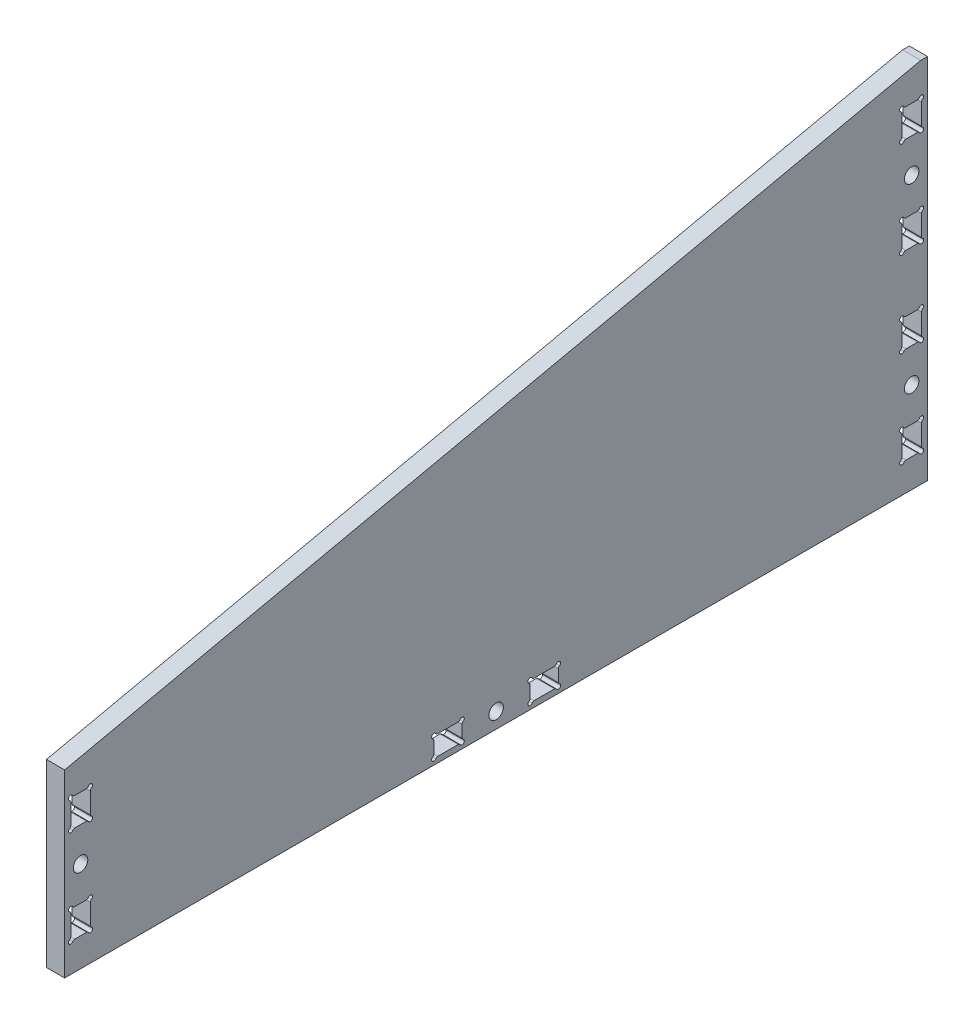
SolidWorks part; units mm, degrees
ref_plane "Alzado" through (0, 0, 0) normal (0, 0, 1) x (1, 0, 0)
ref_plane "Planta" through (0, 0, 0) normal (0, 1, 0) x (1, 0, 0)
ref_plane "Vista lateral" through (0, 0, 0) normal (1, 0, 0) x (0, 0, -1)
sketch "Croquis1" plane through (0, 0, 0) normal (1, 0, 0) x (0, 0, -1)
  line L0 (-94.8108, -1.6532) -> (93.6893, 39.3945)
  line L2 (95.1893, -41.4778) -> (-94.8108, -41.3254)
  line L4 (-1.4107, -37.9765) -> (1.7893, -37.9765) construction
  line L5 (0.1893, -41.4016) -> (0.1893, 19.0339) construction
  line L6 (-91.3108, -20.0603) -> (-91.3108, -22.5929) construction
  line L7 (-93.3108, -21.3266) -> (-89.3108, -21.3266) construction
  line L8 (91.6893, 19.7897) -> (91.6893, 17.2571) construction
  line L9 (89.6893, 18.5234) -> (93.6893, 18.5234) construction
  line L10 (89.6893, -21.4766) -> (93.6893, -21.4766) construction
  line L11 (91.6893, -20.2103) -> (91.6893, -22.7429) construction
  line L12 (13.8893, -36.6926) -> (13.8893, -39.2605)
  line L13 (-93.4607, -8.4926) -> (-93.4607, -12.9606)
  line L22 (-8.1768, -40.1265) -> (-12.6447, -40.1265)
  line L23 (7.6893, -39.2605) -> (7.6893, -36.6926)
  line L24 (-13.5107, -39.2605) -> (-13.5107, -36.6926)
  line L25 (0.1893, -39.9765) -> (0.1893, -35.9765) construction
  line L26 (13.0232, -40.1265) -> (8.5553, -40.1265)
  line L27 (-12.6447, -35.8266) -> (-8.1768, -35.8266)
  line L28 (-7.3107, -36.6926) -> (-7.3107, -39.2605)
  line L29 (8.5553, -35.8266) -> (13.0232, -35.8266)
  line L30 (-94.8108, -41.3266) -> (-94.8108, -1.6532)
  line L31 (95.1893, 39.3945) -> (95.1893, -41.4778)
  line L32 (-90.0268, -13.8266) -> (-92.5947, -13.8266)
  line L34 (93.6893, 39.3945) -> (95.1893, 39.3945)
  line L35 (-89.3108, -21.3266) -> (-93.3108, -21.3266) construction
  line L36 (-92.5947, -7.6266) -> (-90.0268, -7.6266)
  line L40 (-90.0268, -35.0266) -> (-92.5947, -35.0266)
  line L41 (-92.5947, -28.8266) -> (-90.0268, -28.8266)
  line L42 (92.9733, 26.0234) -> (90.4054, 26.0234)
  line L43 (89.5394, 5.6894) -> (89.5394, 10.1574)
  line L44 (93.6893, 18.5234) -> (89.6893, 18.5234) construction
  line L45 (90.4054, 32.2234) -> (92.9733, 32.2234)
  line L46 (89.5394, 26.8894) -> (89.5394, 31.3574)
  line L47 (93.8393, 31.3574) -> (93.8393, 26.8894)
  line L48 (93.8393, 10.1574) -> (93.8393, 5.6894)
  line L49 (92.9733, 4.8234) -> (90.4054, 4.8234)
  line L50 (90.4054, 11.0234) -> (92.9733, 11.0234)
  line L51 (92.9733, -13.9766) -> (90.4054, -13.9766)
  line L52 (89.5394, -34.3106) -> (89.5394, -29.8426)
  line L53 (93.6893, -21.4766) -> (89.6893, -21.4766) construction
  line L54 (90.4054, -7.7766) -> (92.9733, -7.7766)
  line L55 (89.5394, -13.1106) -> (89.5394, -8.6426)
  line L56 (93.8393, -8.6426) -> (93.8393, -13.1106)
  line L57 (93.8393, -29.8426) -> (93.8393, -34.3106)
  line L58 (92.9733, -35.1766) -> (90.4054, -35.1766)
  line L59 (90.4054, -28.9766) -> (92.9733, -28.9766)
  line L60 (-93.4607, -29.6926) -> (-93.4607, -34.1606)
  line L61 (-89.1608, -8.4926) -> (-89.1608, -12.9606)
  line L62 (-89.1608, -29.6926) -> (-89.1608, -34.1606)
  arc A26 (8.5553, -40.1265) -> (8.1223, -40.3765) centre (8.5553, -40.6265) ccw
  arc A27 (8.1223, -35.5766) -> (7.4393, -36.2596) centre (7.6893, -35.8266) ccw
  arc A28 (-12.6447, -40.1265) -> (-13.0777, -40.3765) centre (-12.6447, -40.6265) ccw
  arc A29 (-13.7607, -39.6935) -> (-13.5107, -39.2605) centre (-14.0107, -39.2605) ccw
  arc A30 (7.4393, -39.6935) -> (8.1223, -40.3765) centre (7.6893, -40.1265) ccw
  arc A31 (-7.0607, -36.2596) -> (-7.3107, -36.6926) centre (-6.8107, -36.6926) ccw
  arc A32 (7.4393, -39.6935) -> (7.6893, -39.2605) centre (7.1893, -39.2605) ccw
  circle A33 centre (0.1893, -37.9765) radius 1.6
  arc A34 (7.6893, -36.6926) -> (7.4393, -36.2596) centre (7.1893, -36.6926) ccw
  circle A35 centre (0.1893, -37.9765) radius 2.8 construction
  arc A36 (-8.1768, -35.8266) -> (-7.7437, -35.5766) centre (-8.1768, -35.3266) ccw
  arc A37 (-7.7437, -40.3765) -> (-7.0607, -39.6935) centre (-7.3107, -40.1265) ccw
  arc A38 (8.1223, -35.5766) -> (8.5553, -35.8266) centre (8.5553, -35.3266) ccw
  arc A39 (-7.7437, -40.3765) -> (-8.1768, -40.1265) centre (-8.1768, -40.6265) ccw
  arc A40 (14.1393, -36.2596) -> (13.4563, -35.5766) centre (13.8893, -35.8266) ccw
  arc A41 (14.1393, -36.2596) -> (13.8893, -36.6926) centre (14.3893, -36.6926) ccw
  arc A42 (13.8893, -39.2605) -> (14.1393, -39.6935) centre (14.3893, -39.2605) ccw
  arc A43 (-7.3107, -39.2605) -> (-7.0607, -39.6935) centre (-6.8107, -39.2605) ccw
  arc A44 (-13.0777, -35.5766) -> (-12.6447, -35.8266) centre (-12.6447, -35.3266) ccw
  arc A45 (13.4563, -40.3765) -> (13.0232, -40.1265) centre (13.0232, -40.6265) ccw
  arc A46 (-13.5107, -36.6926) -> (-13.7607, -36.2596) centre (-14.0107, -36.6926) ccw
  arc A47 (13.4563, -40.3765) -> (14.1393, -39.6935) centre (13.8893, -40.1265) ccw
  arc A48 (-13.0777, -35.5766) -> (-13.7607, -36.2596) centre (-13.5107, -35.8266) ccw
  arc A49 (13.0232, -35.8266) -> (13.4563, -35.5766) centre (13.0232, -35.3266) ccw
  arc A50 (-7.0607, -36.2596) -> (-7.7437, -35.5766) centre (-7.3107, -35.8266) ccw
  arc A51 (-13.7607, -39.6935) -> (-13.0777, -40.3765) centre (-13.5107, -40.1265) ccw
  arc A52 (-93.0277, -28.5766) -> (-93.7107, -29.2596) centre (-93.4607, -28.8266) ccw
  arc A53 (-93.4607, -8.4926) -> (-93.7107, -8.0596) centre (-93.9607, -8.4926) ccw
  arc A54 (-90.0268, -28.8266) -> (-89.5938, -28.5766) centre (-90.0268, -28.3266) ccw
  arc A55 (-89.5938, -35.2766) -> (-88.9108, -34.5936) centre (-89.1608, -35.0266) ccw
  circle A56 centre (-91.3108, -21.3266) radius 1.6
  arc A57 (-88.9108, -8.0596) -> (-89.1608, -8.4926) centre (-88.6608, -8.4926) ccw
  arc A58 (-92.5947, -13.8266) -> (-93.0277, -14.0766) centre (-92.5947, -14.3266) ccw
  arc A59 (-93.0277, -7.3766) -> (-92.5947, -7.6266) centre (-92.5947, -7.1266) ccw
  arc A60 (-88.9108, -29.2596) -> (-89.1608, -29.6926) centre (-88.6608, -29.6926) ccw
  arc A61 (-93.7107, -34.5936) -> (-93.4607, -34.1606) centre (-93.9607, -34.1606) ccw
  arc A62 (-89.5938, -14.0766) -> (-88.9108, -13.3936) centre (-89.1608, -13.8266) ccw
  arc A63 (-93.4607, -29.6926) -> (-93.7107, -29.2596) centre (-93.9607, -29.6926) ccw
  arc A64 (-93.0277, -7.3766) -> (-93.7107, -8.0596) centre (-93.4607, -7.6266) ccw
  arc A65 (-92.5947, -35.0266) -> (-93.0277, -35.2766) centre (-92.5947, -35.5266) ccw
  arc A66 (-93.0277, -28.5766) -> (-92.5947, -28.8266) centre (-92.5947, -28.3266) ccw
  arc A67 (-88.9108, -8.0596) -> (-89.5938, -7.3766) centre (-89.1608, -7.6266) ccw
  arc A68 (-89.5938, -35.2766) -> (-90.0268, -35.0266) centre (-90.0268, -35.5266) ccw
  arc A69 (-89.1608, -34.1606) -> (-88.9108, -34.5936) centre (-88.6608, -34.1606) ccw
  arc A70 (-88.9108, -29.2596) -> (-89.5938, -28.5766) centre (-89.1608, -28.8266) ccw
  circle A71 centre (-91.3108, -21.3266) radius 2.8 construction
  arc A72 (-89.1608, -12.9606) -> (-88.9108, -13.3936) centre (-88.6608, -12.9606) ccw
  arc A73 (-89.5938, -14.0766) -> (-90.0268, -13.8266) centre (-90.0268, -14.3266) ccw
  arc A74 (-93.7107, -13.3936) -> (-93.0277, -14.0766) centre (-93.4607, -13.8266) ccw
  arc A75 (-90.0268, -7.6266) -> (-89.5938, -7.3766) centre (-90.0268, -7.1266) ccw
  arc A76 (-93.7107, -34.5936) -> (-93.0277, -35.2766) centre (-93.4607, -35.0266) ccw
  arc A77 (-93.7107, -13.3936) -> (-93.4607, -12.9606) centre (-93.9607, -12.9606) ccw
  arc A78 (89.9724, 11.2734) -> (89.2894, 10.5904) centre (89.5394, 11.0234) ccw
  arc A79 (89.5394, 31.3574) -> (89.2894, 31.7904) centre (89.0394, 31.3574) ccw
  arc A80 (92.9733, 11.0234) -> (93.4063, 11.2734) centre (92.9733, 11.5234) ccw
  arc A81 (93.4063, 4.5734) -> (94.0893, 5.2564) centre (93.8393, 4.8234) ccw
  circle A82 centre (91.6893, 18.5234) radius 1.6
  arc A83 (94.0893, 31.7904) -> (93.8393, 31.3574) centre (94.3393, 31.3574) ccw
  arc A84 (90.4054, 26.0234) -> (89.9724, 25.7734) centre (90.4054, 25.5234) ccw
  arc A85 (89.9724, 32.4734) -> (90.4054, 32.2234) centre (90.4054, 32.7234) ccw
  arc A86 (94.0893, 10.5904) -> (93.8393, 10.1574) centre (94.3393, 10.1574) ccw
  arc A87 (89.2894, 5.2564) -> (89.5394, 5.6894) centre (89.0394, 5.6894) ccw
  arc A88 (93.4063, 25.7734) -> (94.0893, 26.4564) centre (93.8393, 26.0234) ccw
  arc A89 (89.5394, 10.1574) -> (89.2894, 10.5904) centre (89.0394, 10.1574) ccw
  arc A90 (89.9724, 32.4734) -> (89.2894, 31.7904) centre (89.5394, 32.2234) ccw
  arc A91 (90.4054, 4.8234) -> (89.9724, 4.5734) centre (90.4054, 4.3234) ccw
  arc A92 (89.9724, 11.2734) -> (90.4054, 11.0234) centre (90.4054, 11.5234) ccw
  arc A93 (94.0893, 31.7904) -> (93.4063, 32.4734) centre (93.8393, 32.2234) ccw
  arc A94 (93.4063, 4.5734) -> (92.9733, 4.8234) centre (92.9733, 4.3234) ccw
  arc A95 (93.8393, 5.6894) -> (94.0893, 5.2564) centre (94.3393, 5.6894) ccw
  arc A96 (94.0893, 10.5904) -> (93.4063, 11.2734) centre (93.8393, 11.0234) ccw
  circle A97 centre (91.6893, 18.5234) radius 2.8 construction
  arc A98 (93.8393, 26.8894) -> (94.0893, 26.4564) centre (94.3393, 26.8894) ccw
  arc A99 (93.4063, 25.7734) -> (92.9733, 26.0234) centre (92.9733, 25.5234) ccw
  arc A100 (89.2894, 26.4564) -> (89.9724, 25.7734) centre (89.5394, 26.0234) ccw
  arc A101 (92.9733, 32.2234) -> (93.4063, 32.4734) centre (92.9733, 32.7234) ccw
  arc A102 (89.2894, 5.2564) -> (89.9724, 4.5734) centre (89.5394, 4.8234) ccw
  arc A103 (89.2894, 26.4564) -> (89.5394, 26.8894) centre (89.0394, 26.8894) ccw
  arc A104 (89.9724, -28.7266) -> (89.2894, -29.4096) centre (89.5394, -28.9766) ccw
  arc A105 (89.5394, -8.6426) -> (89.2894, -8.2096) centre (89.0394, -8.6426) ccw
  arc A106 (92.9733, -28.9766) -> (93.4063, -28.7266) centre (92.9733, -28.4766) ccw
  arc A107 (93.4063, -35.4266) -> (94.0893, -34.7436) centre (93.8393, -35.1766) ccw
  circle A108 centre (91.6893, -21.4766) radius 1.6
  arc A109 (94.0893, -8.2096) -> (93.8393, -8.6426) centre (94.3393, -8.6426) ccw
  arc A110 (90.4054, -13.9766) -> (89.9724, -14.2266) centre (90.4054, -14.4766) ccw
  arc A111 (89.9724, -7.5266) -> (90.4054, -7.7766) centre (90.4054, -7.2766) ccw
  arc A112 (94.0893, -29.4096) -> (93.8393, -29.8426) centre (94.3393, -29.8426) ccw
  arc A113 (89.2894, -34.7436) -> (89.5394, -34.3106) centre (89.0394, -34.3106) ccw
  arc A114 (93.4063, -14.2266) -> (94.0893, -13.5436) centre (93.8393, -13.9766) ccw
  arc A115 (89.5394, -29.8426) -> (89.2894, -29.4096) centre (89.0394, -29.8426) ccw
  arc A116 (89.9724, -7.5266) -> (89.2894, -8.2096) centre (89.5394, -7.7766) ccw
  arc A117 (90.4054, -35.1766) -> (89.9724, -35.4266) centre (90.4054, -35.6766) ccw
  arc A118 (89.9724, -28.7266) -> (90.4054, -28.9766) centre (90.4054, -28.4766) ccw
  arc A119 (94.0893, -8.2096) -> (93.4063, -7.5266) centre (93.8393, -7.7766) ccw
  arc A120 (93.4063, -35.4266) -> (92.9733, -35.1766) centre (92.9733, -35.6766) ccw
  arc A121 (93.8393, -34.3106) -> (94.0893, -34.7436) centre (94.3393, -34.3106) ccw
  arc A122 (94.0893, -29.4096) -> (93.4063, -28.7266) centre (93.8393, -28.9766) ccw
  circle A123 centre (91.6893, -21.4766) radius 2.8 construction
  arc A124 (93.8393, -13.1106) -> (94.0893, -13.5436) centre (94.3393, -13.1106) ccw
  arc A125 (93.4063, -14.2266) -> (92.9733, -13.9766) centre (92.9733, -14.4766) ccw
  arc A126 (89.2894, -13.5436) -> (89.9724, -14.2266) centre (89.5394, -13.9766) ccw
  arc A127 (92.9733, -7.7766) -> (93.4063, -7.5266) centre (92.9733, -7.2766) ccw
  arc A128 (89.2894, -34.7436) -> (89.9724, -35.4266) centre (89.5394, -35.1766) ccw
  arc A129 (89.2894, -13.5436) -> (89.5394, -13.1106) centre (89.0394, -13.1106) ccw
  point P0 (-93.3108, -1.3266)
  point P2 (93.6893, -41.4766)
  point P3 (-93.3108, -41.3266)
  point P143 (-94.8108, -1.3266)
extrude "Saliente-Extruir1" add sketch "Croquis1" along normal blind 4 contours L34 L0 L30 L2 L31 A128 A113 L52 A115 A104 A118 L59 A106 A122 A112 L57 A121 A107 A120 L58 A117 A108 A102 A87 L43 A89 A78 A92 L50 A80 A96 A86 L48 A95 A81 A94 L49 A91 A82 A76 A61 L60 A63 A52 A66 L41
